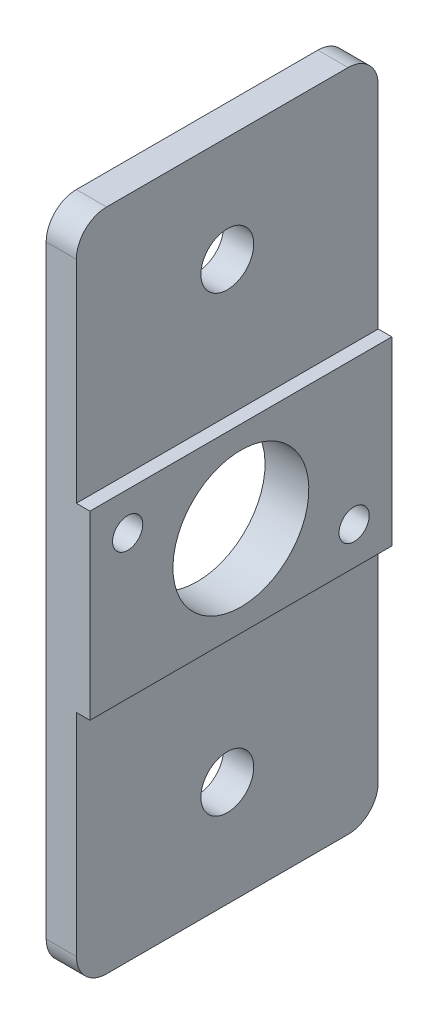
SolidWorks part; units mm, degrees
ref_plane "Front Plane" through (0, 0, 0) normal (0, 0, 1) x (1, 0, 0)
ref_plane "Top Plane" through (0, 0, 0) normal (0, 1, 0) x (1, 0, 0)
ref_plane "Right Plane" through (0, 0, 0) normal (1, 0, 0) x (0, 0, -1)
sketch "Sketch1" plane through (0, 0, 0) normal (0, 0, 1) x (1, 0, 0)
  line L0 (0, 0) -> (0, -44)
  line L1 (0, -44) -> (2, -44)
  line L2 (2, -44) -> (2, -28)
  line L3 (2, -28) -> (2.9, -28)
  line L4 (2.9, -28) -> (2.9, -16)
  line L5 (2.9, -16) -> (2, -16)
  line L6 (2, -16) -> (2, 0)
  line L7 (2, 0) -> (0, 0)
  line L8 (0, -22) -> (52.7304, -22) construction
  point P11 (2.9, -22)
  dimension "D1" = 2
  dimension "D2" = 44
  dimension "D3" = 12
  dimension "D4" = 0.9
extrude "Boss-Extrude1" add sketch "Sketch1" along normal blind 20
sketch "Sketch2" plane through (0, 0, 0) normal (-1, 0, 0) x (0, 0, 1)
  line L0 (10, 0) -> (10, -44) construction
  line L1 (20, 0) -> (0, 0) construction
  line L2 (20, -44) -> (0, -44) construction
  circle A0 centre (10, -7) radius 1.75
  circle A1 centre (10, -37) radius 1.75
  circle A2 centre (10, -22) radius 4.5
  dimension "D3" = 9
  dimension "D4" = 3.5
  dimension "D5" = 3.5
  dimension "D1" = 7
  dimension "D2" = 7
extrude "Cut-Extrude1" cut sketch "Sketch2" against normal through all
sketch "Sketch3" plane through (2.9, 0, 0) normal (1, 0, 0) x (0, 0, -1)
  line L0 (-20, -16) -> (0, -16) construction
  line L1 (-20, -28) -> (-20, -16) construction
  line L2 (0, -28) -> (0, -16) construction
  line L3 (-20, -28) -> (0, -28) construction
  circle A0 centre (-17.5, -18.5) radius 1
  circle A1 centre (-2.5, -25.5) radius 1
  dimension "D5" = 2
  dimension "D6" = 2
  dimension "D1" = 2.5
  dimension "D2" = 2.5
  dimension "D3" = 2.5
  dimension "D4" = 2.5
extrude "Cut-Extrude2" cut sketch "Sketch3" against normal blind 1.8
fillet "Fillet1" radius 2 4 edges at (1, -44, 20) (1, -44, 0) (1, 0, 0) (1, 0, 20)
